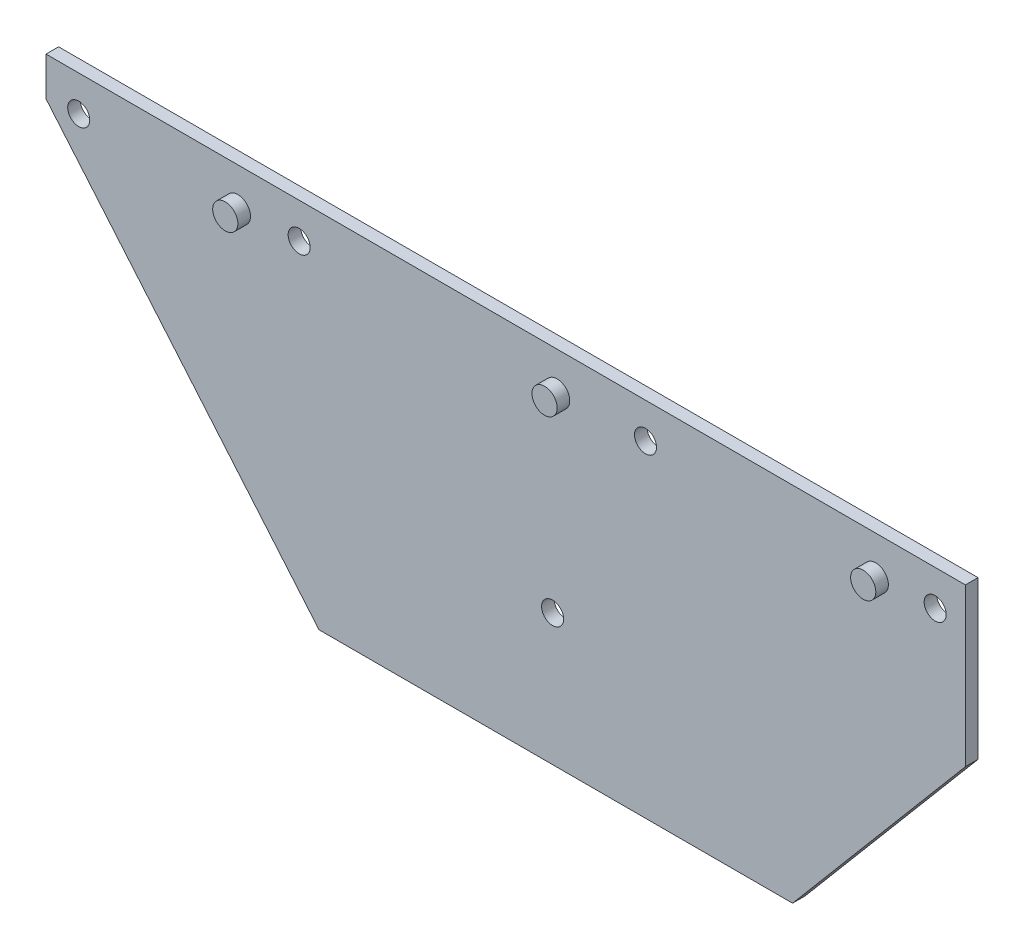
SolidWorks part; units mm, degrees
ref_plane "Plano frontal" through (0, 0, 0) normal (0, 0, 1) x (1, 0, 0)
ref_plane "Plano superior" through (0, 0, 0) normal (0, 1, 0) x (1, 0, 0)
ref_plane "Plano direito" through (0, 0, 0) normal (1, 0, 0) x (0, 0, -1)
sketch "Esboço1" plane through (0, 0, 0) normal (0, 0, 1) x (1, 0, 0)
  line L0 (-73, 22.5898) -> (-29.6452, -28.75)
  line L1 (-29.6452, -28.75) -> (45.5548, -28.75)
  line L2 (-73, 22.5898) -> (-73, 28.75)
  line L3 (-73, 28.75) -> (73, 28.75)
  line L4 (73, 3.75) -> (73, 28.75)
  line L5 (-73, -28.75) -> (73, 28.75) construction
  line L6 (-73, 28.75) -> (73, -28.75) construction
  line L7 (73, 3.75) -> (45.5548, -28.75)
  point P0 (0, 0)
  dimension "D1" = 146
  dimension "D2" = 57.5
  dimension "D3" = 25
  dimension "D4" = 130.18
  dimension "D5" = 130.18
  dimension "D6" = 75.2
extrude "Ressalto-extrusão1" add sketch "Esboço1" along normal blind 2
sketch "Esboço2" plane through (0, 0, 2) normal (0, 0, 1) x (1, 0, 0)
  line L0 (73, 3.75) -> (73, 28.75) construction
  line L1 (73, 28.75) -> (-73, 28.75) construction
  circle A0 centre (22.2, 23.13) radius 1.75
  circle A1 centre (68.2, 23.13) radius 1.75
  circle A2 centre (-32.8, 23.13) radius 1.75
  circle A3 centre (-67.8, 23.13) radius 1.75
  circle A4 centre (7.45, -7.87) radius 1.75
  dimension "D1" = 55
  dimension "D2" = 46
  dimension "D3" = 90
  dimension "D4" = 4.8
  dimension "D5" = 5.62
  dimension "D6" = 31
  dimension "D7" = 14.75
extrude "Corte-extrusão1" cut sketch "Esboço2" against normal up to next
sketch "Esboço3" plane through (0, 0, 2) normal (0, 0, 1) x (1, 0, 0)
  line L0 (73, 3.75) -> (73, 28.75) construction
  circle A0 centre (8.17, 22.662) radius 2
  circle A1 centre (58.77, 22.662) radius 2
  circle A2 centre (-42.53, 22.662) radius 2
  dimension "D1" = 50.7
  dimension "D2" = 50.6
  dimension "D3" = 64.83
extrude "Ressalto-extrusão2" add sketch "Esboço3" along normal blind 2
